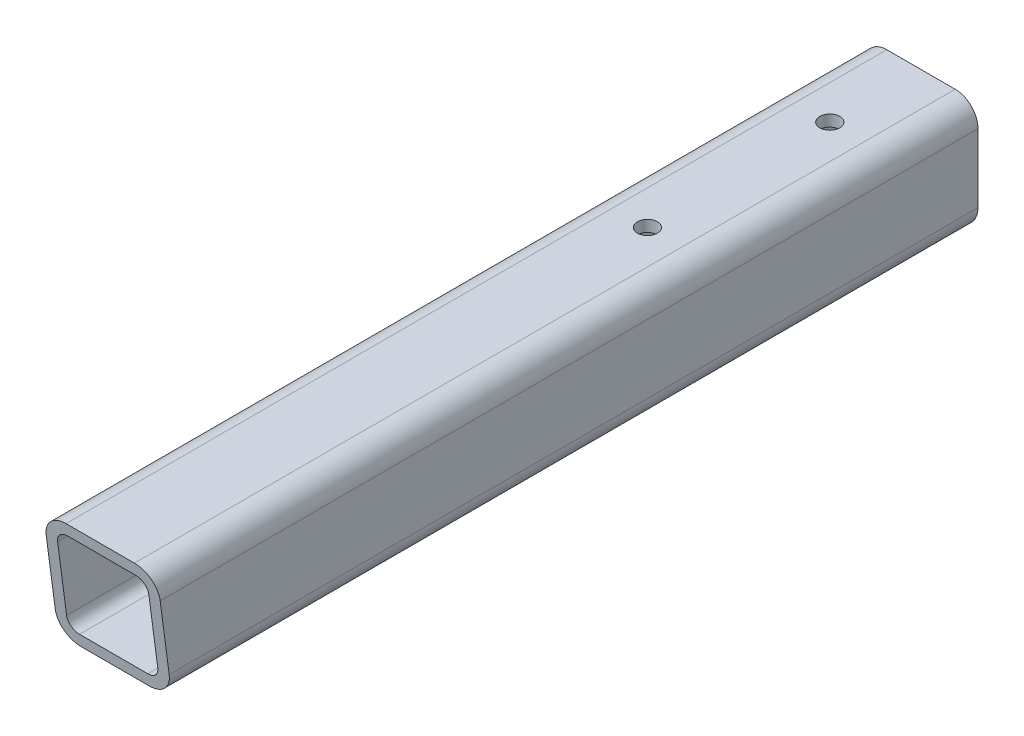
SolidWorks part; units mm, degrees
ref_plane "Front Plane" through (0, 0, 0) normal (0, 0, 1) x (1, 0, 0)
ref_plane "Top Plane" through (0, 0, 0) normal (0, 1, 0) x (1, 0, 0)
ref_plane "Right Plane" through (0, 0, 0) normal (1, 0, 0) x (0, 0, -1)
sketch "Sketch1" plane through (0, 0, 0) normal (0, 0, 1) x (1, 0, 0)
  line L0 (-19.05, -25.4) -> (19.05, -25.4)
  line L1 (-25.4, -19.05) -> (-25.4, 19.05)
  line L2 (19.05, 25.4) -> (-19.05, 25.4)
  line L3 (25.4, 19.05) -> (25.4, -19.05)
  line L4 (-19.05, -31.75) -> (19.05, -31.75)
  line L5 (-31.75, -19.05) -> (-31.75, 19.05)
  line L6 (19.05, 31.75) -> (-19.05, 31.75)
  line L7 (31.75, 19.05) -> (31.75, -19.05)
  line L10 (-25.4, 0) -> (25.4, 0)
  arc A0 (31.75, 19.05) -> (19.05, 31.75) centre (19.05, 19.05) ccw
  arc A1 (19.05, -31.75) -> (31.75, -19.05) centre (19.05, -19.05) ccw
  arc A2 (-31.75, -19.05) -> (-19.05, -31.75) centre (-19.05, -19.05) ccw
  arc A3 (-19.05, 31.75) -> (-31.75, 19.05) centre (-19.05, 19.05) ccw
  arc A4 (-19.05, 25.4) -> (-25.4, 19.05) centre (-19.05, 19.05) ccw
  arc A5 (25.4, 19.05) -> (19.05, 25.4) centre (19.05, 19.05) ccw
  arc A6 (19.05, -25.4) -> (25.4, -19.05) centre (19.05, -19.05) ccw
  arc A7 (-25.4, -19.05) -> (-19.05, -25.4) centre (-19.05, -19.05) ccw
extrude "Boss-Extrude1" add sketch "Sketch1" along normal mid plane 457.2 contours L6 A3 L5 A2 L4 A1 L7 A0 A7 L1 A4 L2 A5 L3 A6 L0
sketch "Sketch3" plane through (0, 31.75, 0) normal (0, 1, 0) x (1, 0, 0)
  line L0 (19.05, 228.6) -> (-19.05, 228.6) construction
  line L1 (0, -34.925) -> (0, 34.925) construction
  circle A0 centre (0, 177.8) radius 5.5562
  circle A1 centre (0, 76.2) radius 5.5562
  dimension "D3" = 11.1125
  dimension "D1" = 101.6
  dimension "D2" = 50.8
extrude "Cut-Extrude1" cut sketch "Sketch3" against normal through all
sketch "Sketch4" plane through (31.75, 0, 0) normal (1, 0, 0) x (0, 0, -1)
  line L0 (-228.6, 31.75) -> (228.6, 31.75) construction
  line L1 (-228.6, 31.75) -> (228.6, 31.75)
  line L2 (-228.6, 31.75) -> (-228.6, -114.2669)
  line L3 (-228.6, -114.2669) -> (-209.3765, -114.2669)
  line L4 (-209.3765, -114.2669) -> (-228.6, 31.75)
  line M2 (228.6, 19.05) -> (-228.6, 19.05)
  line M3 (-228.6, 19.05) -> (-228.6, -19.05)
  line M4 (-228.6, -19.05) -> (228.6, -19.05)
  dimension "D1" = 7.5
extrude "Cut-Extrude2" cut sketch "Sketch4" against normal through all contours L3 L4 L2 M4 | L4 M4 M2 M3 | L4 L2 M2
